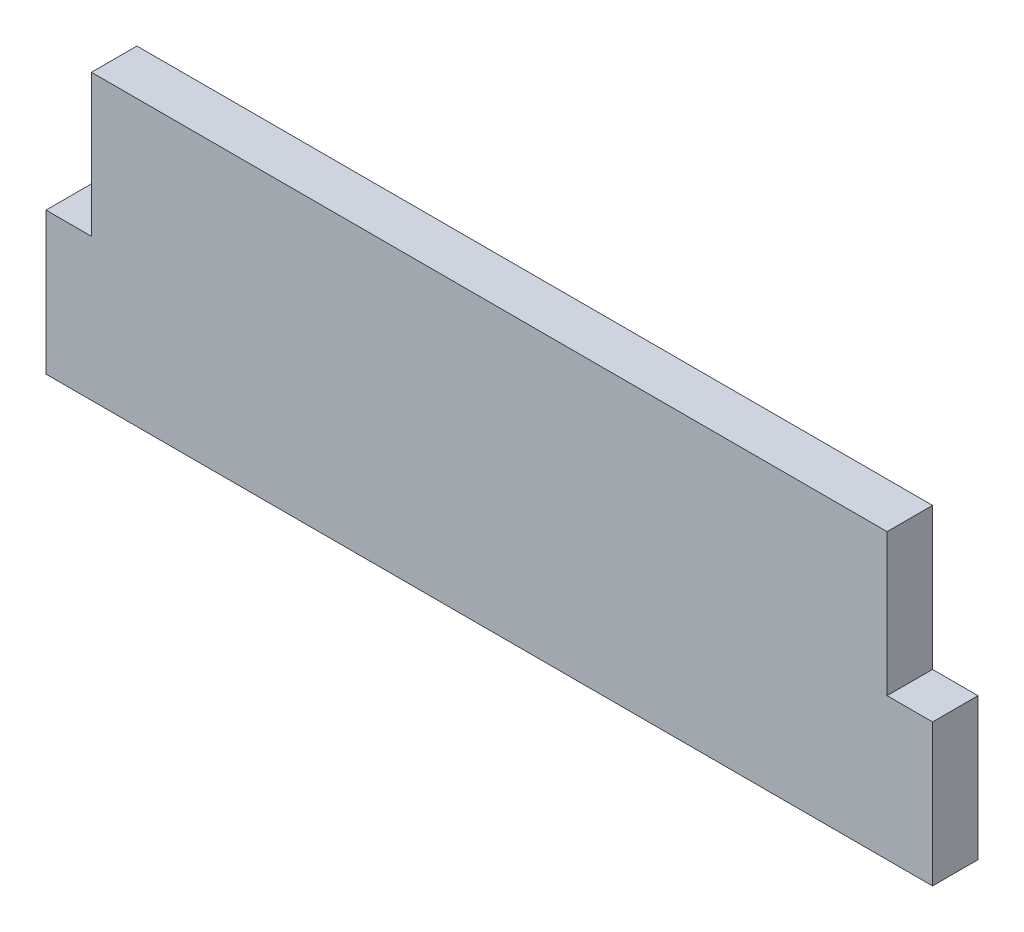
SolidWorks part; units mm, degrees
ref_plane "Front Plane" through (0, 0, 0) normal (0, 0, 1) x (1, 0, 0)
ref_plane "Top Plane" through (0, 0, 0) normal (0, 1, 0) x (1, 0, 0)
ref_plane "Right Plane" through (0, 0, 0) normal (1, 0, 0) x (0, 0, -1)
sketch "Sketch2" plane through (0, 0, 0) normal (0, 0, 1) x (1, 0, 0)
  line L0 (-44.45, 0) -> (-44.45, -15.875)
  line L1 (44.45, -15.875) -> (-44.45, -15.875)
  line L2 (44.45, -15.875) -> (44.45, 15.875)
  line L3 (44.45, 15.875) -> (-44.45, 15.875)
  line L4 (-44.45, -15.875) -> (-44.45, 15.875)
  line L5 (44.45, -15.875) -> (-44.45, 15.875) construction
  line L6 (44.45, 15.875) -> (-44.45, -15.875) construction
  line L7 (-44.45, 0) -> (-49.53, 0)
  line L8 (-44.45, -15.875) -> (-49.53, -15.875)
  line L9 (-49.53, 0) -> (-49.53, -15.875)
  line L10 (44.45, 0) -> (44.45, -15.875)
  line L11 (44.45, 0) -> (49.53, 0)
  line L12 (44.45, -15.875) -> (49.53, -15.875)
  line L13 (49.53, 0) -> (49.53, -15.875)
  point P0 (0, 0)
  dimension "D1" = 88.9
  dimension "D2" = 31.75
  dimension "D3" = 5.08
extrude "Boss-Extrude1" add sketch "Sketch2" along normal blind 5.08 contours L7 L9 L8 L0 | L4 L0 L1 L2 L3 | L13 L11 L2 L12
